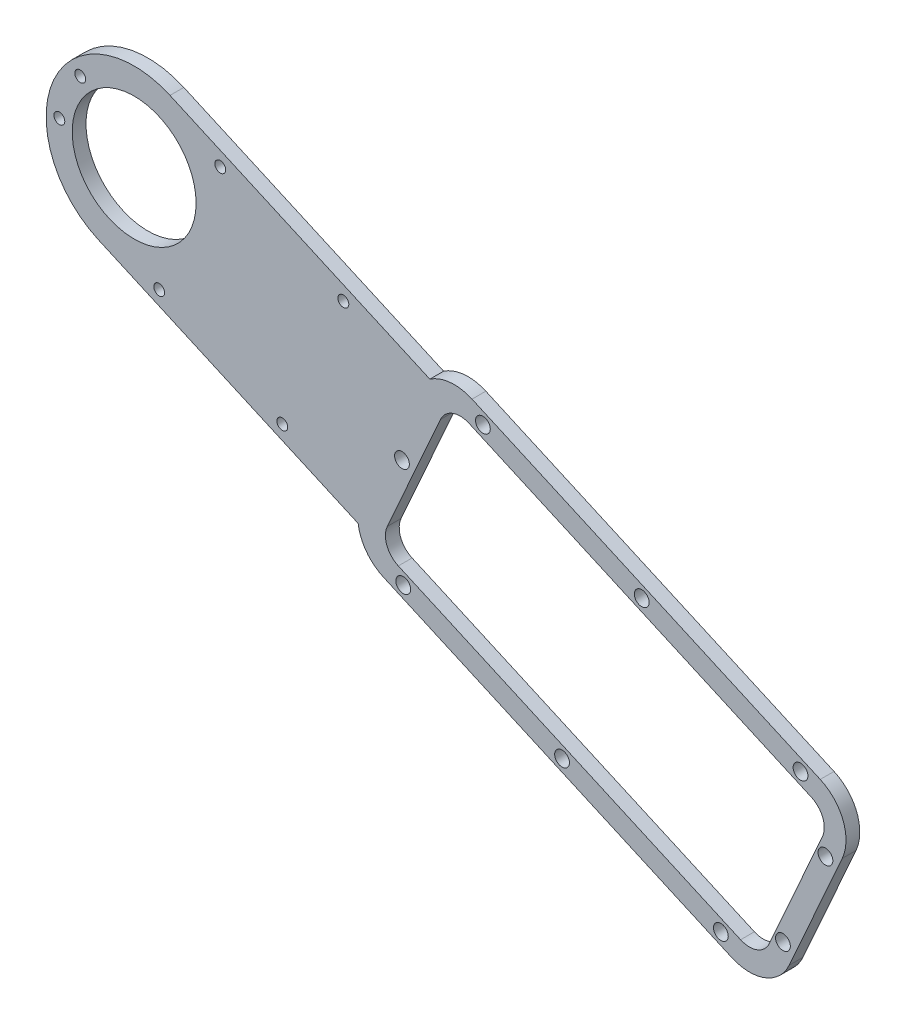
SolidWorks part; units mm, degrees
ref_plane "Front Plane" through (0, 0, 0) normal (0, 0, 1) x (1, 0, 0)
ref_plane "Top Plane" through (0, 0, 0) normal (0, 1, 0) x (1, 0, 0)
ref_plane "Right Plane" through (0, 0, 0) normal (1, 0, 0) x (0, 0, -1)
ref_plane "Plane1" through (0, 0, 0) normal (0, 0, -1) x (-1, 0, 0)
sketch "Sketch1" plane through (0, 0, 0) normal (0, 0, -1) x (-1, 0, 0)
  line L0 (67.6532, 77.6322) -> (79.8678, 50.2314)
  line L1 (93.0729, 45.1693) -> (173.1746, 80.8766)
  line L2 (179.0143, 88.6803) -> (238.789, 115.3263)
  line L3 (222.2994, 152.3174) -> (162.5246, 125.6714)
  line L4 (152.817, 126.5446) -> (72.7153, 90.8373)
  line L5 (74.7511, 86.2705) -> (153.4928, 121.3715)
  line L6 (160.0954, 118.8405) -> (172.3099, 91.4397)
  line L7 (169.7789, 84.8371) -> (91.0372, 49.7361)
  line L8 (84.4346, 52.2672) -> (72.22, 79.668)
  circle A0 centre (168.9326, 106.3571) radius 1.7
  circle A1 centre (71.5234, 76.0729) radius 1.7
  circle A2 centre (81.2951, 54.1522) radius 1.7
  circle A3 centre (77.2496, 90.1215) radius 1.7
  circle A4 centre (113.784, 106.4076) radius 1.7
  circle A5 centre (150.3184, 122.6936) radius 1.7
  circle A6 centre (168.6403, 81.5924) radius 1.7
  circle A7 centre (132.1059, 65.3063) radius 1.7
  circle A8 centre (95.5715, 49.0202) radius 1.7
  circle A9 centre (230.5442, 133.8219) radius 14.25
  arc A10 (79.8678, 50.2314) -> (93.0729, 45.1693) centre (89.0014, 54.3029) ccw
  arc A11 (173.1746, 80.8766) -> (179.0143, 88.6803) centre (169.1031, 90.0102) ccw
  arc A12 (238.789, 115.3263) -> (222.2994, 152.3174) centre (230.5442, 133.8219) ccw
  arc A13 (162.5246, 125.6714) -> (152.817, 126.5446) centre (156.8885, 117.411) ccw
  arc A14 (72.7153, 90.8373) -> (67.6532, 77.6322) centre (76.7868, 81.7037) ccw
  circle A15 centre (196.4664, 99.7446) radius 1.25
  circle A16 centre (224.7805, 112.3663) radius 1.25
  circle A17 centre (210.7338, 143.8772) radius 1.25
  circle A18 centre (182.4196, 131.2555) radius 1.25
  circle A19 centre (242.9474, 145.8104) radius 1.25
  circle A20 centre (247.7516, 135.033) radius 1.25
  arc A21 (72.22, 79.668) -> (74.7511, 86.2705) centre (76.7868, 81.7037) cw
  arc A22 (153.4928, 121.3715) -> (160.0954, 118.8405) centre (155.5286, 116.8047) cw
  arc A23 (172.3099, 91.4397) -> (169.7789, 84.8371) centre (167.7431, 89.4039) cw
  arc A24 (91.0372, 49.7361) -> (84.4346, 52.2672) centre (89.0014, 54.3029) cw
extrude "Boss-Extrude1" add sketch "Sketch1" against normal blind 3.175
